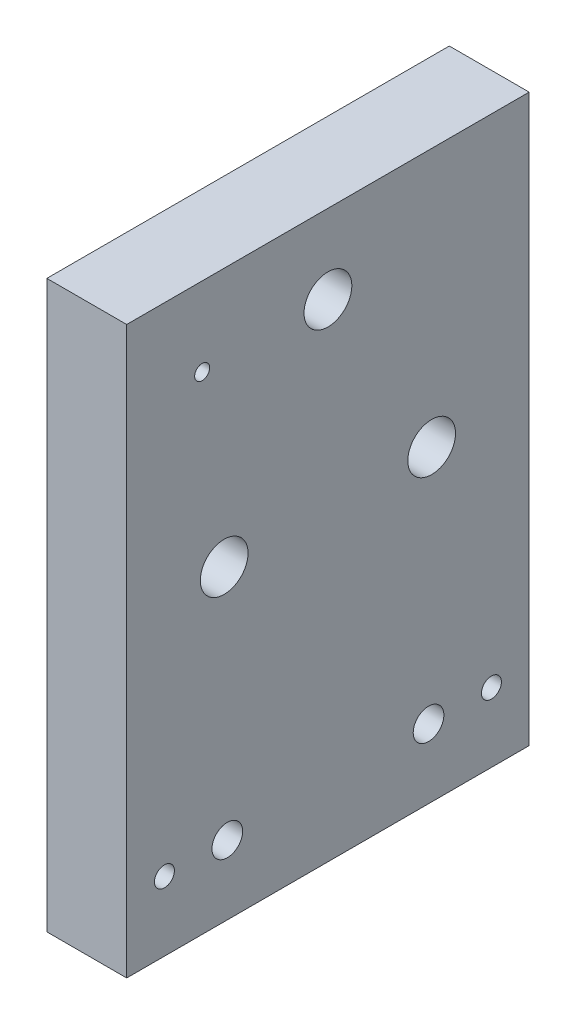
SolidWorks part; units mm, degrees
material "6061-T4 (SS)"
ref_plane "Front Plane" through (0, 0, 0) normal (0, 0, 1) x (1, 0, 0)
ref_plane "Top Plane" through (0, 0, 0) normal (0, 1, 0) x (1, 0, 0)
ref_plane "Right Plane" through (0, 0, 0) normal (1, 0, 0) x (0, 0, -1)
sketch "Sketch1" plane through (0, 0, 0) normal (0, 1, 0) x (1, 0, 0)
  line L1 (-36.5, 16) -> (36.5, 16)
  line L2 (-36.5, 16) -> (-36.5, -16)
  line L3 (-36.5, -16) -> (36.5, -16)
  line L4 (36.5, 16) -> (36.5, -16)
  line L5 (-36.5, 16) -> (36.5, -16) construction
  line L6 (-36.5, -16) -> (36.5, 16) construction
  point P0 (0, 0)
  dimension "D1" = 73
  dimension "D2" = 32
sketch "Sketch26" plane through (0, 0, 0) normal (0, 1, 0) x (-1, 0, 0)
  line L1 (-6.35, 0) -> (0, 0)
  line L2 (-6.35, 0) -> (-6.35, 32)
  line L3 (-6.35, 32) -> (0, 32)
  line L4 (0, 0) -> (0, 32)
  dimension "D1" = 6.35
  dimension "D2" = 32
extrude "Boss-Extrude2" add sketch "Sketch26" along normal blind 45
sketch "Sketch27" plane through (0, 0, 0) normal (-1, 0, 0) x (0, 0, 1)
  line L0 (32, 45) -> (0, 45) construction
  line L1 (0, 45) -> (0, 0) construction
  line L3 (7.7511, 24.4375) -> (24.2489, 24.4375) construction
  line L4 (16, 24.4375) -> (16, 38.725) construction
  line L5 (7.7511, 24.4375) -> (32, 24.4375) construction
  line L7 (24.2489, 24.4375) -> (0, 24.4375) construction
  line L9 (32, 45) -> (32, 0) construction
  circle A0 centre (16, 38.725) radius 1.595
  circle A1 centre (24.2489, 24.4375) radius 1.595
  circle A2 centre (7.7511, 24.4375) radius 1.595
  dimension "D1" = 3.19
  dimension "D2" = 3.19
  dimension "D3" = 3.19
  dimension "D6" = 14.2875
  dimension "D7" = 16.4978
  dimension "D8" = 6.275
extrude "Cut-Extrude7" cut sketch "Sketch27" against normal up to next
hole_wizard "CBORE for #6 Binding Head Machine Screw1" positions "Sketch57" profile "Sketch58" counterbore size "#6" standard "ANSI Inch"
sketch "Sketch57" plane through (0, 0, 0) normal (-1, 0, 0) x (0, 0, 1)
  point P0 (16, 38.725)
  point P3 (24.2489, 24.4375)
  point P6 (7.7511, 24.4375)
sketch "Sketch58" plane through (0, 38.725, 16) normal (0, 1, 0) x (0, 0, 1)
  line L0 (0, 0) -> (0, 47.6408)
  line L1 (0, 47.6408) -> (1.8986, 46.5)
  line L2 (1.8986, 46.5) -> (1.8986, 1.016)
  line L3 (1.8986, 1.016) -> (4.7625, 1.016)
  line L4 (4.7625, 1.016) -> (4.7625, 0)
  line L5 (4.7625, 0) -> (0, 0)
  line L10 (0, 47.6408) -> (-1.8987, 46.5) construction
  line L11 (0, -6.35) -> (0, 107.95) construction
  dimension "Hole Dia." = 3.7973
  dimension "Hole Depth" = 46.5
  dimension "C'Bore Dia." = 9.525
  dimension "C'Bore Depth" = 1.016
  dimension "Drill Angle" = 118
sketch "Sketch88" plane through (0, 0, 0) normal (-1, 0, 0) x (0, 0, 1)
  line L0 (32, 45) -> (32, 0) construction
  line L1 (24.2489, 24.4375) -> (7.7511, 24.4375) construction
  line L2 (16, 24.4375) -> (16, 38.725) construction
  point P0 (32, 22.5)
  point P1 (16, 31.5813)
hole_wizard "#0-80 Tapped Hole1" positions "Sketch93" profile "Sketch94" tap size "#0-80" standard "ANSI Inch" end condition through all
sketch "Sketch93" plane through (0, 0, 0) normal (-1, 0, 0) x (0, 0, 1)
  line L4 (16, 38.725) -> (26, 38.725) construction
  line L5 (26, 38.725) -> (0, 38.725) construction
  line L7 (0, 45) -> (0, 0) construction
  line L8 (32, 45) -> (0, 45) construction
  circle A0 centre (16, 38.725) radius 4.7625 construction
  point P0 (26, 38.725)
  dimension "D1" = 10
  dimension "D2" = 6.275
sketch "Sketch94" plane through (0, 38.725, 26) normal (0, 1, 0) x (0, 0, 1)
  line L0 (0, 0) -> (0, 6.35)
  line L1 (0, 6.35) -> (0.5956, 6.35)
  line L2 (0.5956, 6.35) -> (0.5956, 0)
  line L5 (0.5956, 0) -> (0, 0)
  line L11 (0, -6.35) -> (0, 107.95) construction
  dimension "Thru Tap Drill Dia." = 1.1913
  dimension "Thru Tap Drill Depth" = 6.35
cosmetic thread "Hole Thread1" parameters "D2"=1.524
hole_wizard "#2 Clearance Hole1" positions "Sketch101" profile "Sketch102" hole size "#2" standard "ANSI Inch"
sketch "Sketch101" plane through (0, 0, 0) normal (-1, 0, 0) x (0, 0, 1)
  line L0 (0, 0) -> (32, 0) construction
  line L1 (0, 45) -> (0, 0) construction
  line L2 (32, 5.5) -> (24, 5.5) construction
  line L3 (32, 45) -> (32, 0) construction
  line L4 (24, 5.5) -> (8, 5.5) construction
  line L5 (8, 5.5) -> (0, 5.5) construction
  point P0 (8, 5.5)
  point P3 (24, 5.5)
  dimension "D1" = 5.5
  dimension "D2" = 16
  dimension "D3" = 8
sketch "Sketch102" plane through (0, 5.5, 8) normal (0, 1, 0) x (0, 0, 1)
  line L0 (0, 0) -> (0, 21.0526)
  line L1 (0, 21.0526) -> (1.2192, 20.32)
  line L2 (1.2192, 20.32) -> (1.2192, 0)
  line L5 (1.2192, 0) -> (0, 0)
  line L10 (0, 21.0526) -> (-1.2192, 20.32) construction
  line L11 (0, -6.35) -> (0, 107.95) construction
  dimension "Hole Dia." = 2.4384
  dimension "Hole Depth" = 20.32
  dimension "Drill Angle" = 118
hole_wizard "1/16 (0.0625) Dowel Hole1" positions "Sketch103" profile "Sketch104" hole size "1/16" standard "ANSI Inch"
sketch "Sketch103" plane through (6.35, 0, 0) normal (1, 0, 0) x (0, 0, -1)
  point P0 (-29, 5.5)
  point P2 (-3, 5.5)
sketch "Sketch104" plane through (6.35, 5.5, 29) normal (0, 1, 0) x (0, 0, -1)
  line L0 (0, 0) -> (0, 4)
  line L1 (0, 4) -> (0.7937, 3.5231)
  line L2 (0.7937, 3.5231) -> (0.7937, 0)
  line L5 (0.7937, 0) -> (0, 0)
  line L10 (0, 4) -> (-0.7938, 3.5231) construction
  line L11 (0, -6.35) -> (0, 107.95) construction
  dimension "Hole Dia." = 1.5875
  dimension "Hole Depth" = 4
  dimension "Drill Angle" = 118
